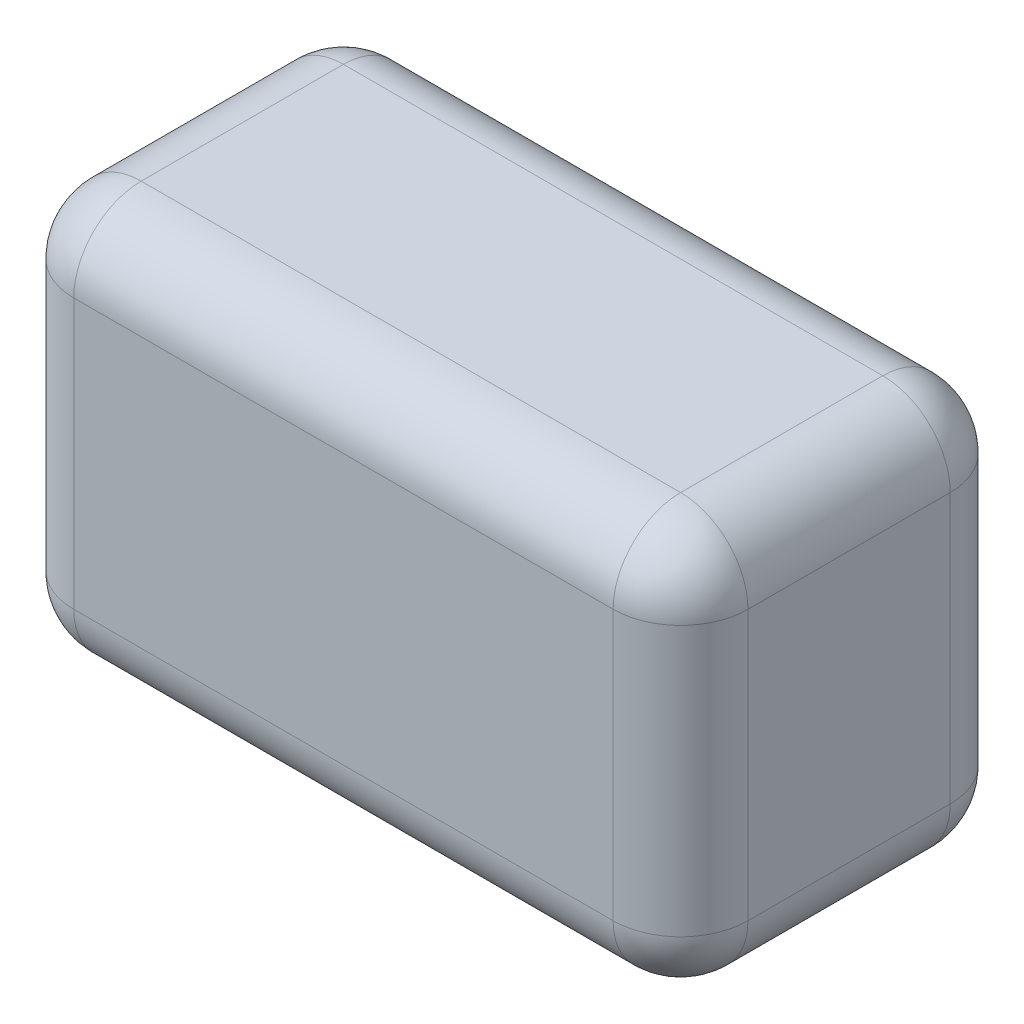
SolidWorks part; units mm, degrees
ref_plane "Front Plane" through (0, 0, 0) normal (0, 0, 1) x (1, 0, 0)
ref_plane "Top Plane" through (0, 0, 0) normal (0, 1, 0) x (1, 0, 0)
ref_plane "Right Plane" through (0, 0, 0) normal (1, 0, 0) x (0, 0, -1)
sketch "Sketch1" plane through (0, 0, 0) normal (0, 1, 0) x (1, 0, 0)
  line L1 (-127, 63.5) -> (127, 63.5)
  line L2 (-127, 63.5) -> (-127, -63.5)
  line L3 (-127, -63.5) -> (127, -63.5)
  line L4 (127, 63.5) -> (127, -63.5)
  line L5 (-127, 63.5) -> (127, -63.5) construction
  line L6 (-127, -63.5) -> (127, 63.5) construction
  point P0 (0, 0)
  dimension "D1" = 127
  dimension "D2" = 254
extrude "Boss-Extrude1" add sketch "Sketch1" along normal blind 152.4
fillet "Fillet1" radius 25.4 12 edges at (127, 0, 0) (127, 76.2, -63.5) (0, 0, -63.5) (-127, 76.2, -63.5) (-127, 0, 0) (-127, 152.4, 0) (0, 152.4, -63.5) (127, 152.4, 0) (-127, 76.2, 63.5) (0, 152.4, 63.5) (127, 76.2, 63.5) (0, 0, 63.5)
sketch "Sketch3" plane through (0, 0, 0) normal (0, -1, 0) x (1, 0, 0)
  circle A0 centre (-50.8, 0) radius 3.81
  point P2 (0, 0)
  dimension "D1" = 50.8
  dimension "D2" = 7.62
extrude "Cut-Extrude1" cut sketch "Sketch3" against normal blind 8.89
mirror "Mirror1" about plane through (0, 0, 0) normal (1, 0, 0) of "Cut-Extrude1"
